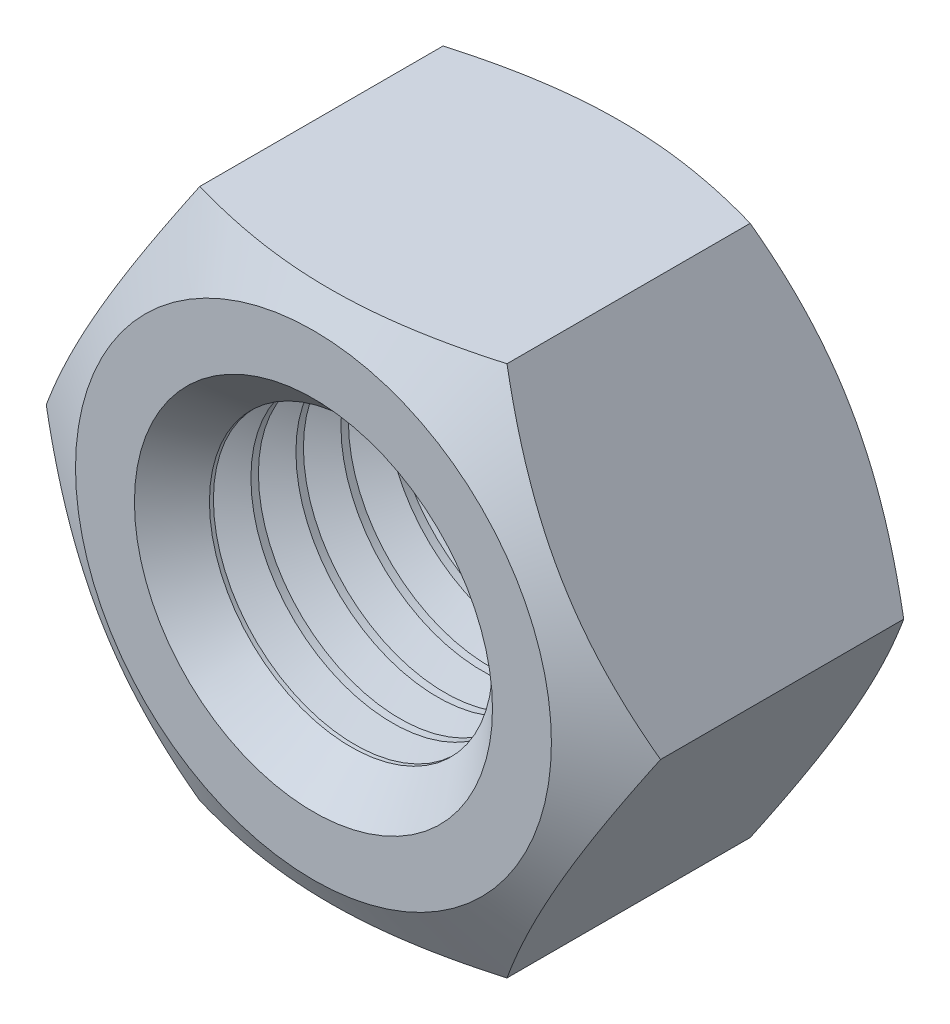
SolidWorks part; units mm, degrees
ref_plane "Front" through (0, 0, 0) normal (0, 0, 1) x (1, 0, 0)
ref_plane "Top" through (0, 0, 0) normal (0, 1, 0) x (1, 0, 0)
ref_plane "Right" through (0, 0, 0) normal (1, 0, 0) x (0, 0, -1)
sketch "Sketch1" plane through (0, 0, 0) normal (0, 0, 1) x (1, 0, 0)
  line L1 (3.7528, -6.5) -> (7.5056, 0)
  line L2 (7.5056, 0) -> (3.7528, 6.5)
  line L3 (3.7528, 6.5) -> (-3.7528, 6.5)
  line L4 (-3.7528, 6.5) -> (-7.5056, 0)
  line L5 (-7.5056, 0) -> (-3.7528, -6.5)
  line L6 (-3.7528, -6.5) -> (3.7528, -6.5)
  circle A0 centre (0, 0) radius 6.5 construction
  circle A1 centre (0, 0) radius 3.4585
  dimension "D1" = 6.917
  dimension "s" = 13
extrude "BaseNut" add sketch "Sketch1" against normal blind 7.5
cosmetic thread "ThreadCosmetic1" [suppressed] parameters "D2"=8.75
sketch "Sketch2" plane through (15.0481, 0, -16.7061) normal (0, 1, 0) x (0, 0, -1)
  line L0 (-23.7227, 15.0481) -> (22.0646, 15.0481) construction
  line L2 (-9.2061, 22.5537) -> (-9.2061, 18.8009) construction
  line L4 (-9.2061, 22.5537) -> (-16.7061, 22.5537) construction
  line L8 (-9.7867, 22.5537) -> (-9.2061, 21.5481)
  line L9 (-9.2061, 22.5537) -> (-9.7867, 22.5537)
  line L10 (-9.2061, 21.5481) -> (-9.2061, 22.5537)
  dimension "D1" = 30
  dimension "s1" = 13
revolve "Chamfer1" cut sketch "Sketch2" angle 360 about L0
sketch "Sketch6" plane through (-9.1975, 0, -10.2525) normal (0, 1, 0) x (0, 0, 1)
  line L0 (23.3574, 9.1975) -> (-22.3023, 9.1975) construction
  line L2 (2.7525, 12.656) -> (2.7525, 13.5725)
  line L4 (2.7525, 13.5725) -> (3.2817, 12.656)
  line L6 (3.2817, 12.656) -> (2.7525, 12.656)
  dimension "da" = 8.75
  dimension "D2" = 60
revolve "EndChamfer1" cut sketch "Sketch6" angle 360 about L0
sketch "Sketch5" plane through (-14.793, 0, -16.9612) normal (0, 1, 0) x (0, 0, 1)
  line L0 (-22.5748, 14.793) -> (24.743, 14.793) construction
  line L2 (16.9612, 20.608) -> (16.9612, 22.2986)
  line L4 (16.9612, 22.2986) -> (15.9852, 22.2986)
  line L6 (15.9852, 22.2986) -> (16.9612, 20.608)
  dimension "dw1" = 11.63
  dimension "D2" = 30
revolve "Chamfer2" cut sketch "Sketch5" angle 360 about L0
sketch "Sketch3" plane through (-20.9491, 1.8856, 0) normal (0, 0, 1) x (1, 0, 0)
  circle A1 centre (20.9491, -1.8856) radius 3.4585 construction
  circle A2 centre (20.9491, -1.8856) radius 5.815
  circle A3 centre (20.9491, -1.8856) radius 3.4585
  dimension "dw" = 11.63
extrude "Extrude1" [suppressed] add sketch "Sketch3" along normal blind 0.6
chamfer "EndChamfer3" [suppressed] distance 0.25 angle 45
chamfer "EndChamfer2" distance 0.9165 angle 45 1 edges at (3.4585, 0, 0)
sketch "Sketch7" plane through (0, 0, 0) normal (0, 1, 0) x (1, 0, 0)
  line L0 (0, 48.6183) -> (0, -13.0076) construction
  line L1 (2.542, 7.4291) -> (3.4585, 7.4291)
  line L2 (3.4585, 7.4291) -> (4.2522, 6.9709)
  line L3 (4.2522, 6.9709) -> (3.4585, 6.5126)
  line L4 (3.4585, 6.5126) -> (2.542, 6.5126)
  line L5 (2.542, 6.5126) -> (2.542, 7.4291)
  line L6 (3.4585, 6.9709) -> (-3.4585, 6.9709) construction
  dimension "D1" = 0.9165
  dimension "D2" = 6.917
revolve "Cut-Revolve10" cut sketch "Sketch7" angle 360 about L0
pattern_linear "LPattern10" count 6 spacing 1.0998 along (0, 0, 1) of "Cut-Revolve10"
equation "\"D1@EndChamfer3\" = \"m@BaseNut\" / 30"
equation "\"s1@Sketch2\" = \"s@Sketch1\""
equation "\"D2@Sketch7\" = \"D1@Sketch1\""
equation "\"D1@Sketch7\" = (  \"D2@ThreadCosmetic1\" - \"D1@Sketch1\" )  / 2"
equation "\"D3@LPattern10\" = \"D1@Sketch7\" * 1.2"
equation "\"D1@LPattern10\" = \"m@BaseNut\" / \"D3@LPattern10\" - 1"
equation "\"D1@EndChamfer2\" = (  \"da@Sketch6\" - \"D1@Sketch1\" )  / 2"
